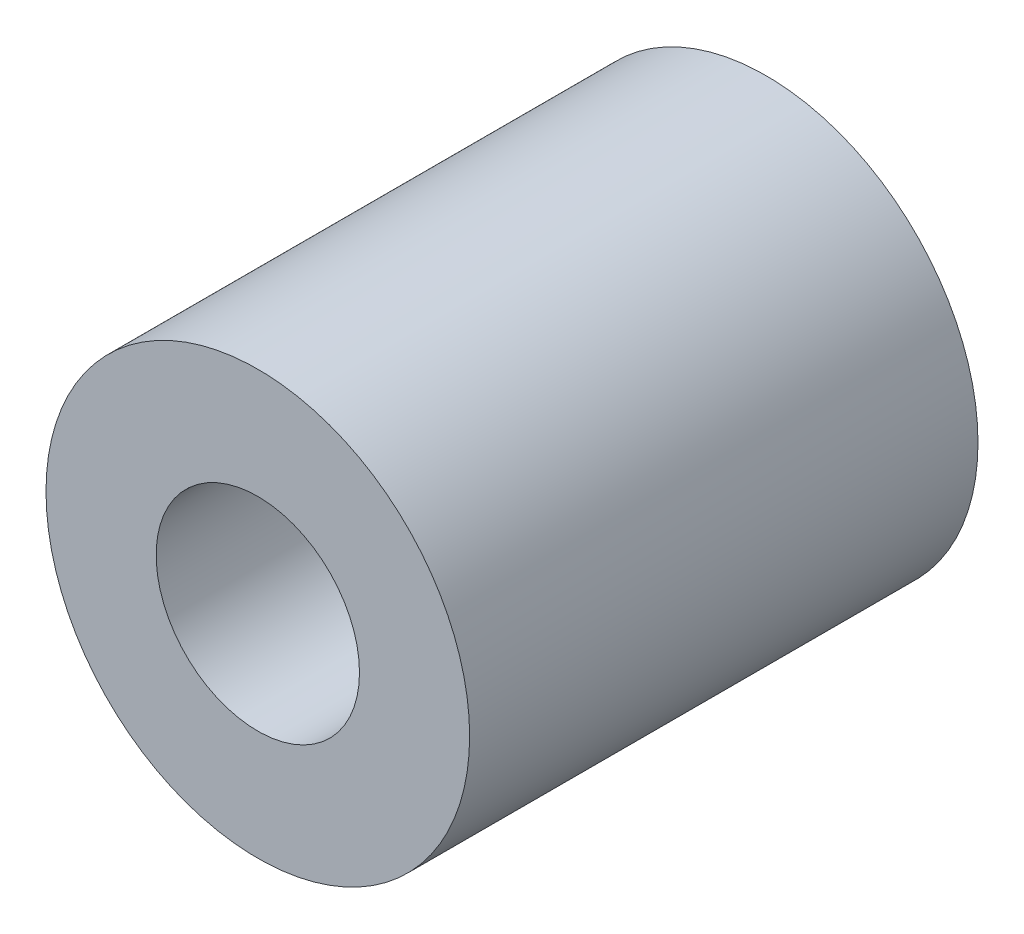
SolidWorks part; units mm, degrees
ref_plane "Front Plane" through (0, 0, 0) normal (0, 0, 1) x (1, 0, 0)
ref_plane "Top Plane" through (0, 0, 0) normal (0, 1, 0) x (1, 0, 0)
ref_plane "Right Plane" through (0, 0, 0) normal (1, 0, 0) x (0, 0, -1)
sketch "Sketch1" plane through (0, 0, 0) normal (0, 0, 1) x (1, 0, 0)
  circle A0 centre (0, 0) radius 12.5
  circle A1 centre (0, 0) radius 6
  dimension "D1" = 25
  dimension "D2" = 12
extrude "Boss-Extrude1" add sketch "Sketch1" along normal blind 30
